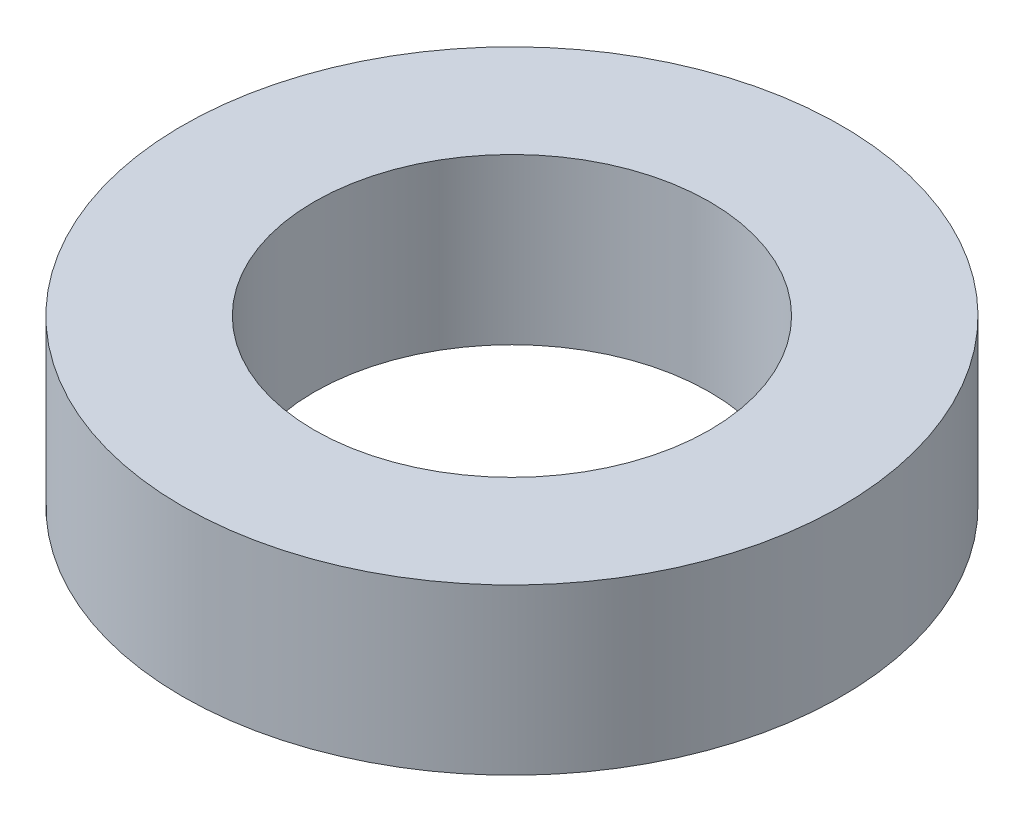
SolidWorks part; units mm, degrees
ref_plane "Front Plane" through (0, 0, 0) normal (0, 0, 1) x (1, 0, 0)
ref_plane "Top Plane" through (0, 0, 0) normal (0, 1, 0) x (1, 0, 0)
ref_plane "Right Plane" through (0, 0, 0) normal (1, 0, 0) x (0, 0, -1)
sketch "Sketch1" plane through (0, 0, 0) normal (0, 1, 0) x (1, 0, 0)
  circle A0 centre (0, 0) radius 6.35
  circle A1 centre (0, 0) radius 3.81
  dimension "D1" = 7.62
  dimension "D2" = 12.7
extrude "Boss-Extrude1" add sketch "Sketch1" along normal blind 3.175
